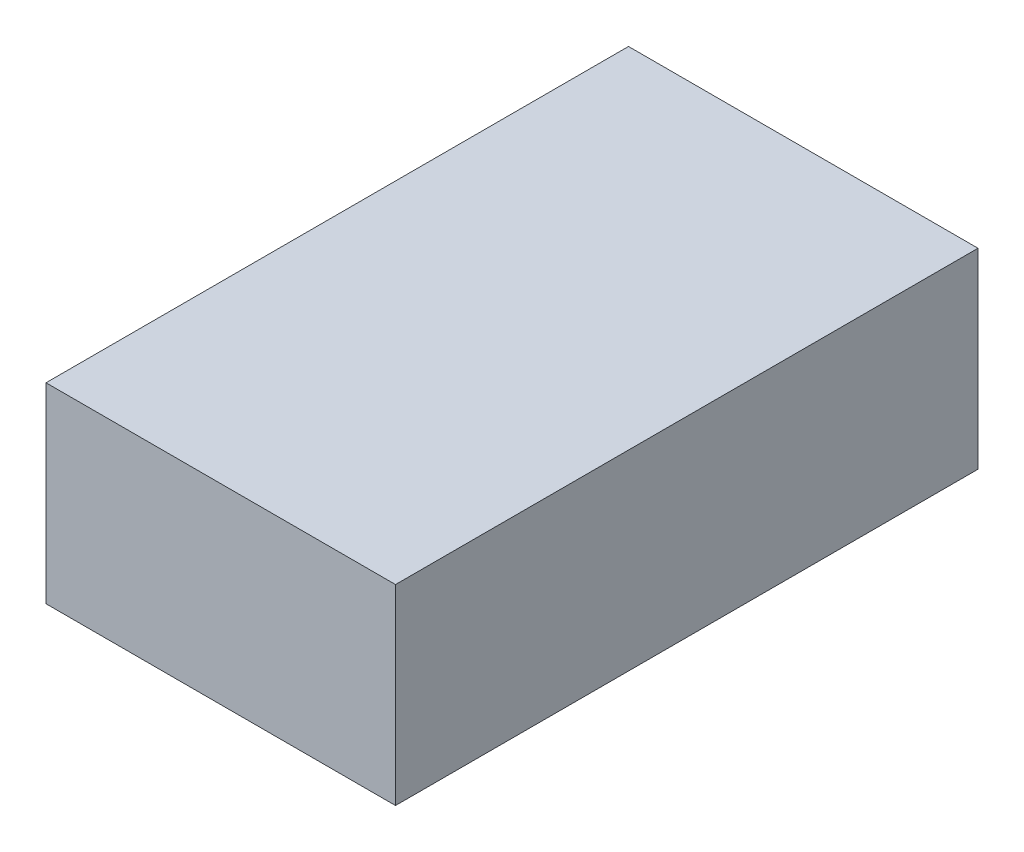
SolidWorks part; units mm, degrees
ref_plane "前视基准面" through (0, 0, 0) normal (0, 0, 1) x (1, 0, 0)
ref_plane "上视基准面" through (0, 0, 0) normal (0, 1, 0) x (1, 0, 0)
ref_plane "右视基准面" through (0, 0, 0) normal (1, 0, 0) x (0, 0, -1)
sketch "草图1" plane through (0, 0, 0) normal (0, 1, 0) x (1, 0, 0)
  line L1 (-10.5, -17.5) -> (10.5, -17.5)
  line L2 (-10.5, -17.5) -> (-10.5, 17.5)
  line L3 (-10.5, 17.5) -> (10.5, 17.5)
  line L4 (10.5, -17.5) -> (10.5, 17.5)
  line L5 (-10.5, -17.5) -> (10.5, 17.5) construction
  line L6 (-10.5, 17.5) -> (10.5, -17.5) construction
  point P0 (0, 0)
  dimension "D1" = 21
  dimension "D2" = 35
extrude "凸台-拉伸1" add sketch "草图1" along normal blind 11.5
